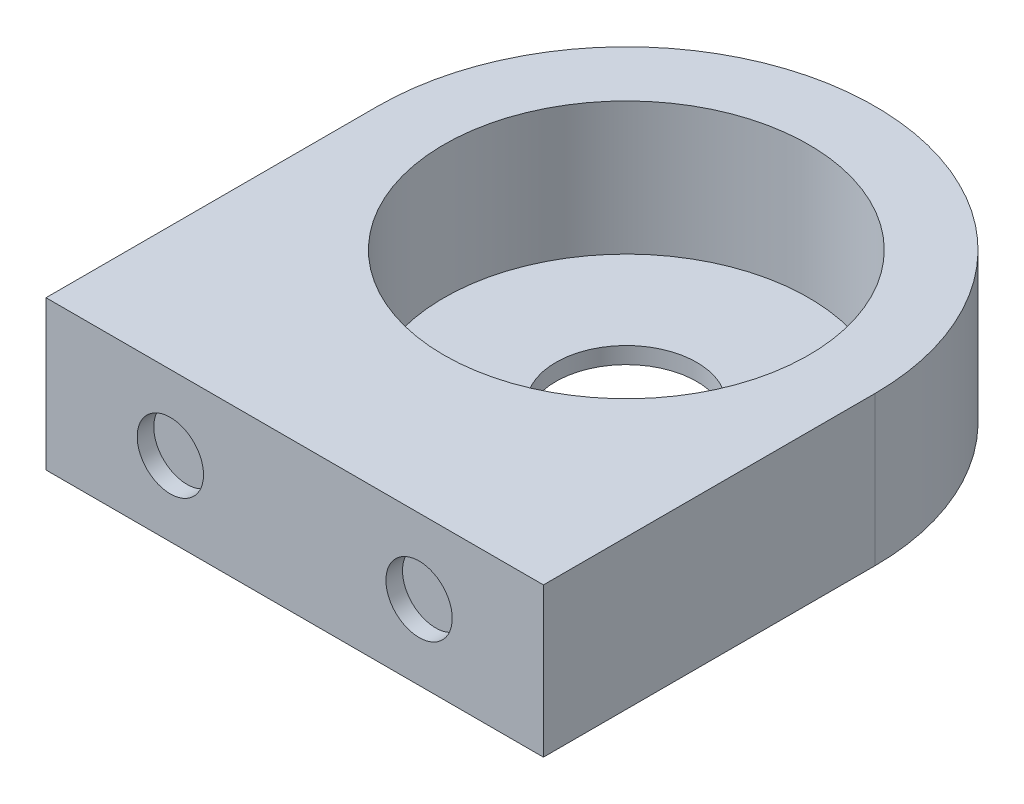
SolidWorks part; units mm, degrees
material "PP Copolymer"
ref_plane "Front Plane" through (0, 0, 0) normal (0, 0, 1) x (1, 0, 0)
ref_plane "Top Plane" through (0, 0, 0) normal (0, 1, 0) x (1, 0, 0)
ref_plane "Right Plane" through (0, 0, 0) normal (1, 0, 0) x (0, 0, -1)
sketch "Sketch1" plane through (0, 0, 0) normal (0, 1, 0) x (1, 0, 0)
  line L0 (30, 0) -> (0, 0)
  line L1 (0, 0) -> (0, 20)
  line L2 (30, 0) -> (30, 20)
  arc A0 (30, 20) -> (0, 20) centre (15, 20) ccw
  circle A1 centre (15, 20) radius 11
  circle A2 centre (15, 20) radius 4.25
  dimension "D1" = 30
  dimension "D3" = 22
  dimension "D4" = 8.5
  dimension "D2" = 20
extrude "Boss-Extrude1" add sketch "Sketch1" along normal blind 9 contours L2 A0 L1 L0 A1 | A1 A2
sketch "Sketch2" plane through (0, 9, 0) normal (0, 1, 0) x (1, 0, 0)
  circle A0 centre (15, 20) radius 11
  circle A1 centre (15, 20) radius 4.25 construction
  dimension "D1" = 22
extrude "Cut-Extrude1" cut sketch "Sketch2" against normal blind 8
sketch "Sketch3" plane through (0, 0, 0) normal (0, 0, 1) x (1, 0, 0)
  line L0 (0, 9) -> (0, 0) construction
  line L3 (15, 4.5) -> (15, 9) construction
  line L4 (0, 4.5) -> (30, 4.5) construction
  line L5 (30, 9) -> (30, 0) construction
  line L6 (30, 9) -> (0, 9) construction
  line L7 (15, 9) -> (15, 0) construction
  line L8 (30, 0) -> (0, 0) construction
  line L9 (15, 4.5) -> (0, 4.5) construction
  line L10 (0, 4.5) -> (15, 4.5) construction
  line L11 (15, 4.5) -> (30, 4.5) construction
  line L12 (30, 4.5) -> (22.5, 4.5) construction
  line L13 (22.5, 4.5) -> (22.5, 9) construction
  line L14 (22.5, 9) -> (22.5, 4.5) construction
  line L15 (22.5, 4.5) -> (7.5, 4.5) construction
  line L16 (7.5, 4.5) -> (7.5, 9) construction
sketch "Sketch4" plane through (0, 0, 0) normal (0, 0, 1) x (1, 0, 0)
  circle A0 centre (7.5, 4.5) radius 2
  circle A1 centre (22.5, 4.5) radius 2
  dimension "D1" = 4
extrude "Cut-Extrude2" cut sketch "Sketch4" against normal blind 1
